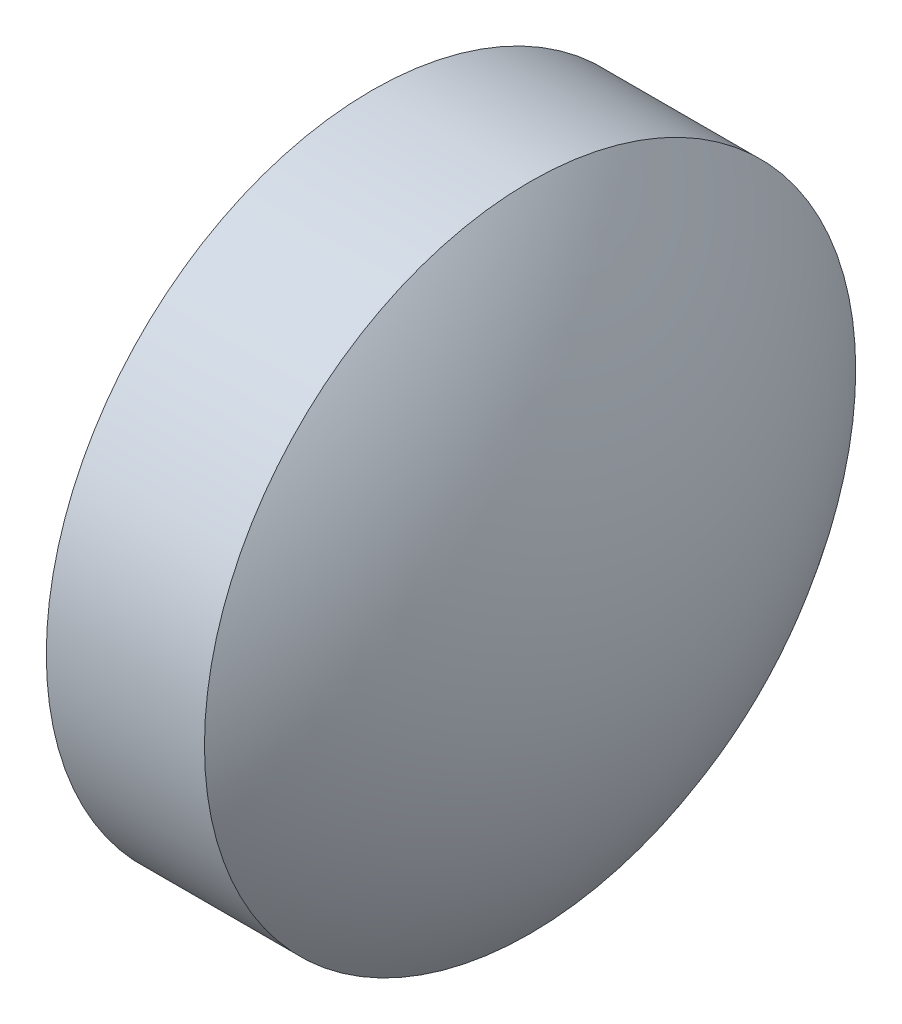
SolidWorks part; units mm, degrees
ref_plane "前视基准面" through (0, 0, 0) normal (0, 0, 1) x (1, 0, 0)
ref_plane "上视基准面" through (0, 0, 0) normal (0, 1, 0) x (1, 0, 0)
ref_plane "右视基准面" through (0, 0, 0) normal (1, 0, 0) x (0, 0, -1)
sketch "草图1" plane through (0, 0, 0) normal (0, 0, 1) x (1, 0, 0)
  line L0 (350.7104, 25.0479) -> (356.8458, 25.0479) construction
  line L1 (351.572, 25.0479) -> (351.572, 28.1979)
  line L2 (354.172, 25.0479) -> (351.572, 25.0479)
  line L5 (351.572, 28.1979) -> (353.102, 28.1979)
  arc A0 (354.172, 25.0479) -> (353.102, 28.1979) centre (349.0004, 25.0479) ccw
revolve "旋转1" add sketch "草图1" angle 360 about L0
